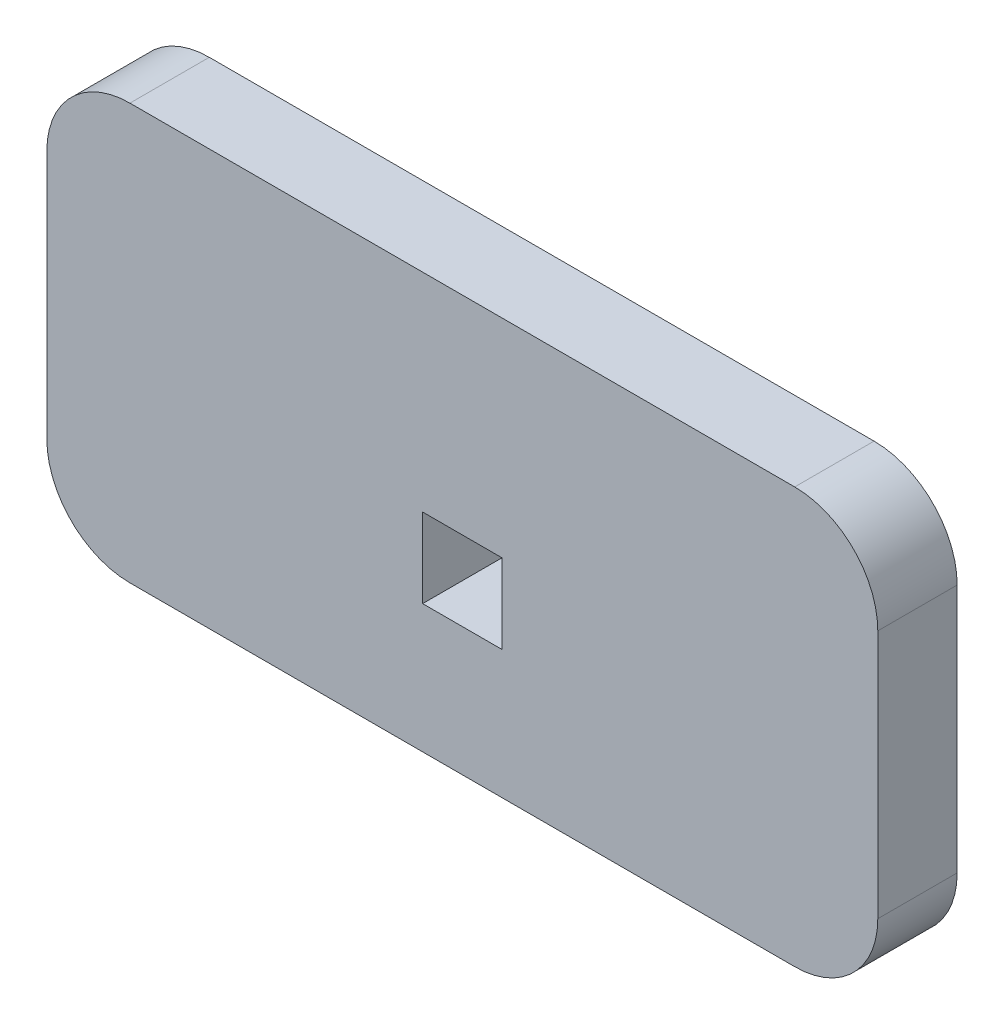
SolidWorks part; units mm, degrees
ref_plane "Front Plane" through (0, 0, 0) normal (0, 0, 1) x (1, 0, 0)
ref_plane "Top Plane" through (0, 0, 0) normal (0, 1, 0) x (1, 0, 0)
ref_plane "Right Plane" through (0, 0, 0) normal (1, 0, 0) x (0, 0, -1)
sketch "Sketch1" plane through (0, 0, 0) normal (0, 0, 1) x (1, 0, 0)
  line L0 (0, 0) -> (50, 0) construction
  line L1 (0, 0) -> (0, -4.7752) construction
  line L2 (5, -4.7752) -> (45, -4.7752)
  line L3 (50, -4.7752) -> (50, 0) construction
  line L4 (0, 0.2248) -> (0, 15.2248)
  line L5 (5, 20.2248) -> (45, 20.2248)
  line L6 (50, 15.2248) -> (50, 0.2248)
  arc A0 (0, 0.2248) -> (5, -4.7752) centre (5, 0.2248) ccw
  arc A1 (45, -4.7752) -> (50, 0.2248) centre (45, 0.2248) ccw
  arc A2 (45, 20.2248) -> (50, 15.2248) centre (45, 15.2248) cw
  arc A3 (0, 15.2248) -> (5, 20.2248) centre (5, 15.2248) cw
  point P17 (0, 20.2248)
  dimension "D4" = 5
  dimension "D1" = 50
  dimension "D2" = 4.7752
  dimension "D3" = 25
extrude "Boss-Extrude1" add sketch "Sketch1" along normal blind 4.7752
sketch "Sketch2" plane through (0, 0, 4.7752) normal (0, 0, 1) x (1, 0, 0)
  line L0 (0, 7.7248) -> (25, 7.7248) construction
  line L1 (0, 15.2248) -> (0, 0.2248) construction
  line L2 (27.3876, 7.7248) -> (22.6124, 7.7248)
  line L3 (22.6124, 2.9496) -> (22.6124, 12.5) construction
  line L4 (25, 7.7248) -> (25, 12.5) construction
  line L5 (27.3876, 2.9496) -> (27.3876, 12.5) construction
  line L6 (22.6124, 12.5) -> (27.3876, 12.5) construction
  line L7 (22.6124, 2.9496) -> (27.3876, 2.9496)
  line L8 (22.6124, 7.7248) -> (22.6124, 2.9496)
  line L9 (27.3876, 7.7248) -> (27.3876, 2.9496)
  dimension "D1" = 25
  dimension "D2" = 2.3876
  dimension "D3" = 4.7752
  dimension "D4" = 4.7752
extrude "Cut-Extrude1" cut sketch "Sketch2" against normal through all
